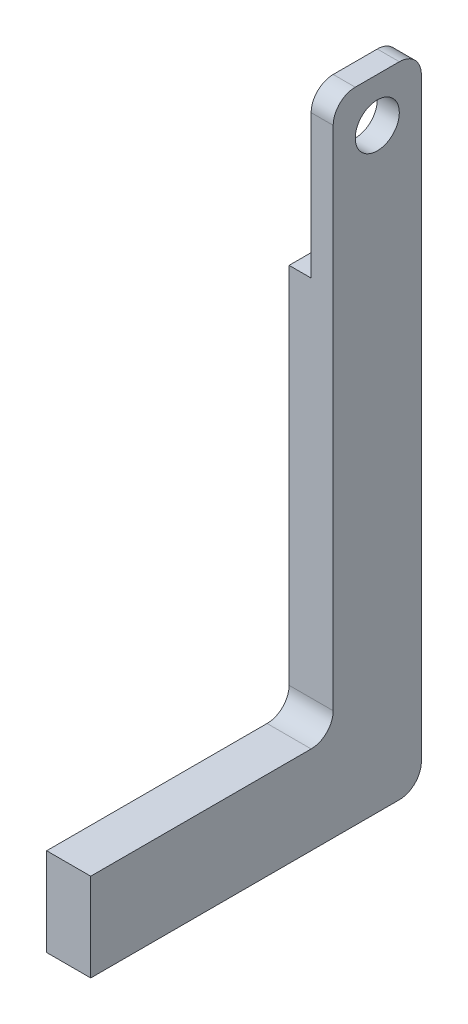
SolidWorks part; units mm, degrees
ref_plane "Ön Düzlem" through (0, 0, 0) normal (0, 0, 1) x (1, 0, 0)
ref_plane "Üst Düzlem" through (0, 0, 0) normal (0, 1, 0) x (1, 0, 0)
ref_plane "Sağ Düzlem" through (0, 0, 0) normal (1, 0, 0) x (0, 0, -1)
sketch "Sketch1" plane through (0, 0, 0) normal (1, 0, 0) x (0, 0, -1)
  line L1 (-20, 125) -> (20, 125)
  line L2 (-20, 125) -> (-20, -125)
  line L3 (-20, -125) -> (20, -125)
  line L4 (20, 125) -> (20, -125)
  line L5 (-20, 125) -> (20, -125) construction
  line L6 (-20, -125) -> (20, 125) construction
  point P0 (0, 0)
  dimension "D1" = 40
  dimension "D2" = 250
extrude "Boss-Extrude1" add sketch "Sketch1" along normal blind 20
sketch "Sketch2" plane through (0, 0, 0) normal (-1, 0, 0) x (0, 0, 1)
  line L0 (-20, -125) -> (-20, 125) construction
  line L1 (20, 125) -> (-20, 125)
  line L2 (20, 125) -> (20, 50)
  line L3 (20, 50) -> (-20, 50)
  line L4 (-20, 125) -> (-20, 50)
  dimension "D1" = 75
extrude "Cut-Extrude1" cut sketch "Sketch2" against normal blind 10
fillet "Fillet1" radius 10 2 edges at (15, 125, -20) (15, 125, 20)
sketch "Sketch3" plane through (20, 0, 0) normal (1, 0, 0) x (0, 0, -1)
  line L0 (10, 125) -> (-10, 125) construction
  circle A0 centre (0, 105) radius 10
  dimension "D1" = 20
extrude "Cut-Extrude2" cut sketch "Sketch3" against normal blind 10
sketch "Sketch5" plane through (0, 0, -20) normal (0, 0, -1) x (-1, 0, 0)
  line L1 (-20, -125) -> (0, -125)
  line L2 (-20, -125) -> (-20, -165)
  line L3 (-20, -165) -> (0, -165)
  line L4 (0, -125) -> (0, -165)
  dimension "D1" = 40
extrude "Boss-Extrude2" add sketch "Sketch5" against normal blind 150
fillet "Fillet2" radius 10 1 edges at (10, -165, -20)
fillet "Fillet3" radius 10 1 edges
